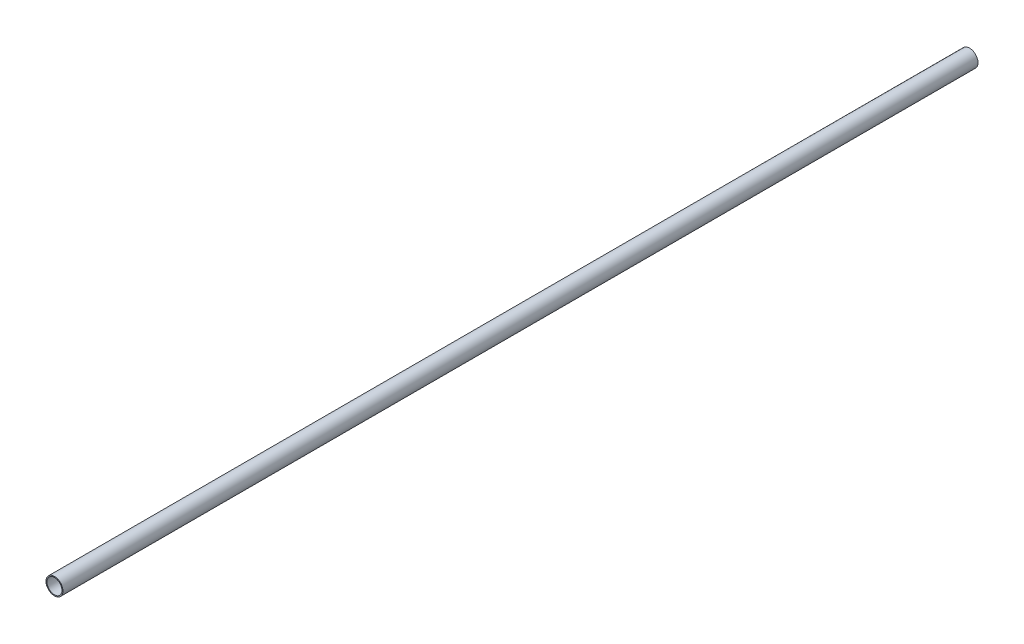
SolidWorks part; units mm, degrees
ref_plane "Front" through (0, 0, 0) normal (0, 0, 1) x (1, 0, 0)
ref_plane "Top" through (0, 0, 0) normal (0, 1, 0) x (1, 0, 0)
ref_plane "Side" through (0, 0, 0) normal (1, 0, 0) x (0, 0, -1)
sketch "PipeSketch" plane through (0, 0, 0) normal (0, 0, 1) x (1, 0, 0)
  circle A0 centre (0, 0) radius 50.8
  circle A1 centre (0, 0) radius 45.0596
  dimension "OuterDiameter" = 101.6
  dimension "InnerDiameter" = 90.1192
extrude "Extrusion" add sketch "PipeSketch" along normal blind 5486.4
sketch "FilterSketch" plane through (0, 0, 0) normal (0, 0, 1) x (1, 0, 0)
  circle A0 centre (0, 0) radius 44.45 construction
  dimension "NominalDiameter" = 88.9
